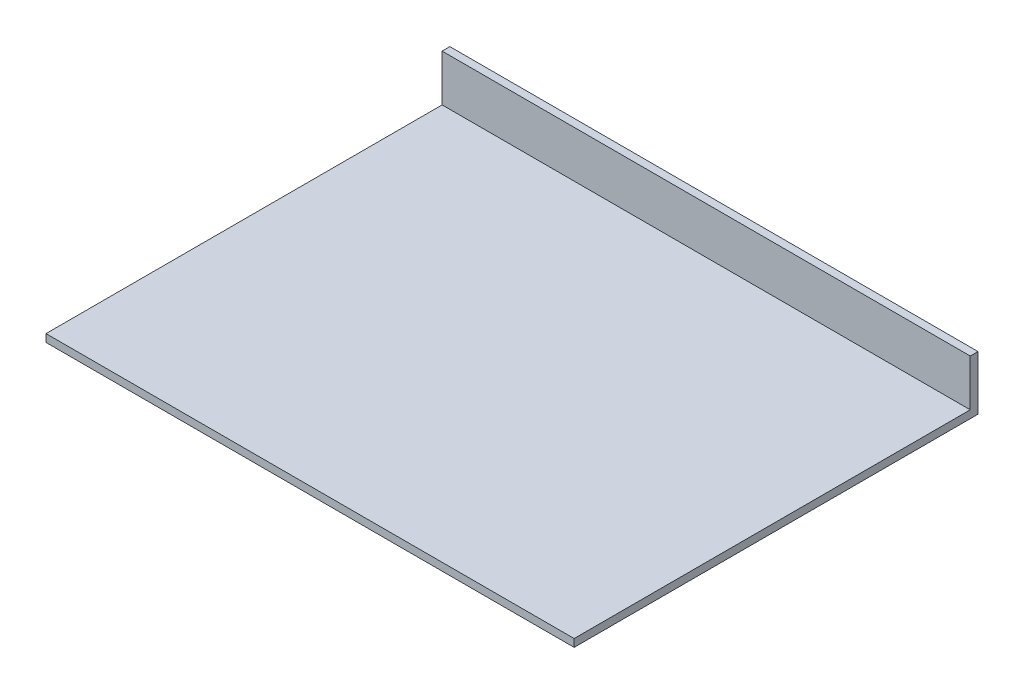
SolidWorks part; units mm, degrees
ref_plane "Front Plane" through (0, 0, 0) normal (0, 0, 1) x (1, 0, 0)
ref_plane "Top Plane" through (0, 0, 0) normal (0, 1, 0) x (1, 0, 0)
ref_plane "Right Plane" through (0, 0, 0) normal (1, 0, 0) x (0, 0, -1)
sketch "Sketch1" plane through (0, 0, 0) normal (0, 1, 0) x (1, 0, 0)
  line L1 (-107.95, -82.55) -> (107.95, -82.55)
  line L2 (-107.95, -82.55) -> (-107.95, 82.55)
  line L3 (-107.95, 82.55) -> (107.95, 82.55)
  line L4 (107.95, -82.55) -> (107.95, 82.55)
  line L5 (-107.95, -82.55) -> (107.95, 82.55) construction
  line L6 (-107.95, 82.55) -> (107.95, -82.55) construction
  point P0 (0, 0)
  dimension "D1" = 215.9
  dimension "D2" = 165.1
extrude "Boss-Extrude3" add sketch "Sketch1" along normal blind 3.1477
sketch "Sketch3" plane through (0, 3.1477, 0) normal (0, 1, 0) x (1, 0, 0)
  line L0 (107.95, -82.55) -> (107.95, 82.55) construction
  line L1 (-107.95, 82.55) -> (107.95, 82.55)
  line L2 (-107.95, 82.55) -> (-107.95, 79.375)
  line L3 (-107.95, 79.375) -> (107.95, 79.375)
  line L4 (107.95, 82.55) -> (107.95, 79.375)
  dimension "D1" = 3.175
extrude "Boss-Extrude4" add sketch "Sketch3" along normal blind 19.05
